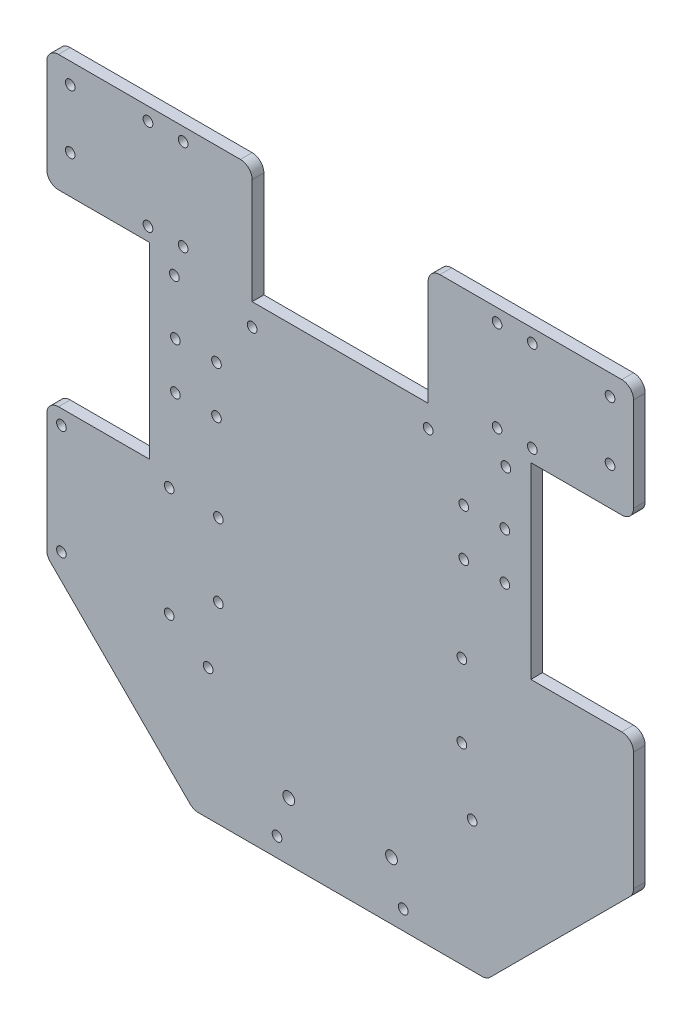
SolidWorks part; units mm, degrees
ref_plane "前视基准面" through (0, 0, 0) normal (0, 0, 1) x (1, 0, 0)
ref_plane "上视基准面" through (0, 0, 0) normal (0, 1, 0) x (1, 0, 0)
ref_plane "右视基准面" through (0, 0, 0) normal (1, 0, 0) x (0, 0, -1)
sketch "草图1" plane through (0, 0, 0) normal (0, 0, 1) x (1, 0, 0)
  line L0 (0, 0) -> (0, 207.9951) construction
  line L1 (-96, 200) -> (-30, 200)
  line L2 (-100, 196) -> (-100, 160)
  line L3 (-50, 0) -> (50, 0)
  line L4 (100, 196) -> (100, 160)
  line L5 (-100, 200) -> (74.6614, 24.6614) construction
  line L6 (-75.1068, 25.1068) -> (100, 200) construction
  line L7 (30, 200) -> (96, 200)
  line L8 (-30, 160) -> (30, 160)
  line L9 (-30, 160) -> (-30, 200)
  line L11 (30, 160) -> (30, 200)
  line L12 (-30, 160) -> (30, 200) construction
  line L13 (-30, 200) -> (30, 160) construction
  line L14 (100, 96) -> (65, 96)
  line L15 (-100, 160) -> (-65, 160)
  line L17 (-100, 96) -> (-65, 96)
  line L18 (-65, 160) -> (-65, 96)
  line L19 (65, 160) -> (65, 96)
  line L20 (100, 160) -> (65, 160)
  line L22 (-100, 96) -> (-100, 50)
  line L23 (100, 96) -> (100, 50)
  line L24 (-100, 50) -> (-50, 0)
  line L25 (100, 50) -> (50, 0)
  arc A0 (96, 200) -> (100, 196) centre (96, 196) cw
  arc A1 (-96, 200) -> (-100, 196) centre (-96, 196) ccw
  point P0 (-0.2545, 99.8678)
  point P7 (0, 180)
  dimension "D9" = 4
  dimension "D1" = 46
  dimension "D2" = 200
  dimension "D3" = 60
  dimension "D4" = 40
  dimension "D5" = 64
  dimension "D6" = 35
  dimension "D7" = 200
  dimension "D8" = 135
extrude "凸台-拉伸1" add sketch "草图1" along normal blind 4
sketch "草图4" plane through (0, 0, 0) normal (0, 0, -1) x (-1, 0, 0)
  line L1 (65, 160) -> (-65, 160) construction
  line L2 (65, 160) -> (65, 39) construction
  line L3 (65, 39) -> (-65, 39) construction
  line L4 (-65, 160) -> (-65, 39) construction
  line L5 (56.5, 154.5) -> (-56.5, 154.5) construction
  line L6 (56.5, 154.5) -> (56.5, 44.5) construction
  line L7 (56.5, 44.5) -> (-56.5, 44.5) construction
  line L8 (-56.5, 154.5) -> (-56.5, 44.5) construction
  line L10 (-30, 160) -> (30, 160) construction
  line L12 (65, 160) -> (65, 96) construction
  line L13 (-65, 96) -> (-65, 160) construction
  line L14 (0, 0) -> (0, 62.8556) construction
  circle A0 centre (56.5, 154.5) radius 1.65
  circle A1 centre (-56.5, 154.5) radius 1.65
  circle A4 centre (45, 44.5) radius 1.65
  circle A5 centre (-45, 44.5) radius 1.65
  dimension "D6" = 3.3
  dimension "D7" = 3.3
  dimension "D1" = 110
  dimension "D2" = 5.5
  dimension "D3" = 8.5
  dimension "D4" = 8.5
  dimension "D5" = 5.5
  dimension "D8" = 90
extrude "切除-拉伸5" cut sketch "草图4" against normal blind 10
sketch "草图5" plane through (0, 0, 0) normal (0, 0, -1) x (-1, 0, 0)
  line L0 (0, 0) -> (0, 78) construction
  line L1 (41.5, 90.5) -> (-41.5, 90.5) construction
  line L2 (41.5, 90.5) -> (41.5, 65.5) construction
  line L3 (41.5, 65.5) -> (-41.5, 65.5) construction
  line L4 (-41.5, 90.5) -> (-41.5, 65.5) construction
  line L5 (41.5, 90.5) -> (-41.5, 65.5) construction
  line L6 (41.5, 65.5) -> (-41.5, 90.5) construction
  line L7 (50, 0) -> (-50, 0) construction
  circle A0 centre (41.5, 90.5) radius 1.65
  circle A1 centre (-41.5, 90.5) radius 1.65
  circle A2 centre (41.5, 65.5) radius 1.65
  circle A3 centre (-41.5, 65.5) radius 1.65
  point P0 (0, 78)
  dimension "D4" = 3.3
  dimension "D1" = 65.5
  dimension "D2" = 83
  dimension "D3" = 25
extrude "切除-拉伸6" cut sketch "草图5" against normal blind 10
sketch "草图6" plane through (0, 0, 0) normal (0, 0, -1) x (-1, 0, 0)
  line L1 (58.26, 91) -> (95, 91) construction
  line L2 (58.26, 91) -> (58.26, 53.62) construction
  line L3 (58.26, 53.62) -> (95, 53.62) construction
  line L4 (95, 91) -> (95, 53.62) construction
  line L5 (65, 96) -> (100, 96) construction
  line L6 (100, 96) -> (100, 50) construction
  circle A1 centre (58.26, 91) radius 1.65
  circle A2 centre (95, 91) radius 1.65
  circle A3 centre (58.26, 53.62) radius 1.65
  circle A4 centre (95, 53.62) radius 1.65
  dimension "D3" = 5
  dimension "D5" = 3.3
  dimension "D1" = 37.38
  dimension "D2" = 36.74
  dimension "D4" = 5
extrude "切除-拉伸7" cut sketch "草图6" against normal blind 10
sketch "草图7" plane through (0, 0, 0) normal (0, 0, -1) x (-1, 0, 0)
  line L0 (0, 0) -> (0, 6.5) construction
  line L1 (50, 0) -> (-50, 0) construction
  line L2 (-21.5, 6.5) -> (21.5, 6.5) construction
  circle A0 centre (-21.5, 6.5) radius 1.65
  circle A1 centre (21.5, 6.5) radius 1.65
  dimension "D3" = 3.3
  dimension "D1" = 6.5
  dimension "D2" = 43
extrude "切除-拉伸8" cut sketch "草图7" against normal blind 10
sketch "草图8" plane through (0, 0, 0) normal (0, 0, -1) x (-1, 0, 0)
  line L0 (0, 0) -> (0, 19.75) construction
  line L1 (-17.5, 19.75) -> (17.5, 19.75) construction
  circle A0 centre (-17.5, 19.75) radius 2
  circle A1 centre (17.5, 19.75) radius 2
  dimension "D3" = 4
  dimension "D1" = 19.75
  dimension "D2" = 35
extrude "切除-拉伸9" cut sketch "草图8" against normal blind 10
sketch "草图9" plane through (0, 0, 0) normal (0, 0, -1) x (-1, 0, 0)
  line L0 (0, 160) -> (0, 152.5) construction
  line L1 (-30, 160) -> (30, 160) construction
  line L2 (-30, 152.5) -> (30, 152.5) construction
  circle A0 centre (-30, 152.5) radius 1.65
  circle A1 centre (30, 152.5) radius 1.65
  dimension "D2" = 3.3
  dimension "D1" = 60
  dimension "D3" = 7.5
extrude "切除-拉伸10" cut sketch "草图9" against normal blind 10
sketch "草图10" plane through (0, 0, 4) normal (0, 0, 1) x (1, 0, 0)
  line L1 (-100, 196) -> (-100, 160) construction
  line L2 (-100, 193) -> (-92, 193) construction
  line L3 (-92, 193) -> (-92, 173) construction
  line L4 (0, 160) -> (0, 0) construction
  line L5 (30, 160) -> (-30, 160) construction
  line L6 (-30, 200) -> (-96, 200) construction
  circle A0 centre (-92, 193) radius 1.65
  circle A1 centre (-92, 173) radius 1.65
  circle A2 centre (92, 173) radius 1.65
  circle A3 centre (92, 193) radius 1.65
  dimension "D3" = 3.3
  dimension "D5" = 3.3
  dimension "D2" = 8
  dimension "D4" = 20
  dimension "D6" = 7
extrude "切除-拉伸11" cut sketch "草图10" against normal blind 10
sketch "草图11" plane through (0, 0, 4) normal (0, 0, 1) x (1, 0, 0)
  line L0 (96, 200) -> (30, 200) construction
  line L1 (65.5, 164.5) -> (53.5, 164.5) construction
  line L2 (65.5, 164.5) -> (65.5, 195.5) construction
  line L3 (65.5, 195.5) -> (53.5, 195.5) construction
  line L4 (53.5, 164.5) -> (53.5, 195.5) construction
  line L5 (65.5, 164.5) -> (53.5, 195.5) construction
  line L6 (65.5, 195.5) -> (53.5, 164.5) construction
  line L7 (30, 200) -> (30, 160) construction
  line L8 (0, 0) -> (0, 212.3238) construction
  line L9 (-50, 0) -> (50, 0) construction
  line L10 (-65.5, 195.5) -> (-53.5, 164.5) construction
  line L11 (-65.5, 164.5) -> (-53.5, 195.5) construction
  line L12 (-53.5, 164.5) -> (-53.5, 195.5) construction
  line L13 (-65.5, 195.5) -> (-53.5, 195.5) construction
  line L15 (-65.5, 164.5) -> (-65.5, 195.5) construction
  line L16 (-65.5, 164.5) -> (-53.5, 164.5) construction
  circle A0 centre (65.5, 164.5) radius 1.65
  circle A1 centre (53.5, 164.5) radius 1.65
  circle A2 centre (53.5, 195.5) radius 1.65
  circle A3 centre (65.5, 195.5) radius 1.65
  circle A8 centre (-65.5, 195.5) radius 1.65
  circle A9 centre (-53.5, 195.5) radius 1.65
  circle A10 centre (-53.5, 164.5) radius 1.65
  circle A11 centre (-65.5, 164.5) radius 1.65
  dimension "D1" = 3.3
  dimension "D2" = 4.5
  dimension "D3" = 31
  dimension "D4" = 12
  dimension "D5" = 23.5
extrude "切除-拉伸12" cut sketch "草图11" against normal blind 10
sketch "草图12" plane through (0, 0, 4) normal (0, 0, 1) x (1, 0, 0)
  line L0 (100, 96) -> (65, 96) construction
  line L1 (56.15, 136) -> (42.15, 136) construction
  line L2 (56.15, 136) -> (56.15, 120) construction
  line L3 (56.15, 120) -> (42.15, 120) construction
  line L4 (42.15, 136) -> (42.15, 120) construction
  line L5 (56.15, 136) -> (42.15, 120) construction
  line L6 (56.15, 120) -> (42.15, 136) construction
  line L8 (100, 160) -> (100, 196) construction
  line L9 (0, 0) -> (0, 113.8804) construction
  line L10 (-50, 0) -> (50, 0) construction
  line L11 (-56.15, 120) -> (-42.15, 136) construction
  line L12 (-56.15, 136) -> (-42.15, 120) construction
  line L13 (-42.15, 136) -> (-42.15, 120) construction
  line L14 (-56.15, 120) -> (-42.15, 120) construction
  line L15 (-56.15, 136) -> (-56.15, 120) construction
  line L16 (-56.15, 136) -> (-42.15, 136) construction
  circle A0 centre (56.15, 120) radius 1.65
  circle A1 centre (42.15, 120) radius 1.65
  circle A2 centre (42.15, 136) radius 1.65
  circle A3 centre (56.15, 136) radius 1.65
  circle A4 centre (-56.15, 136) radius 1.65
  circle A5 centre (-42.15, 136) radius 1.65
  circle A6 centre (-42.15, 120) radius 1.65
  circle A7 centre (-56.15, 120) radius 1.65
  point P0 (49.15, 128)
  point P25 (-49.15, 128)
  dimension "D3" = 3.3
  dimension "D1" = 14
  dimension "D2" = 16
  dimension "D4" = 32
  dimension "D5" = 43.85
extrude "切除-拉伸13" cut sketch "草图12" against normal blind 10
fillet "圆角1" radius 4 8 edges at (100, 96, 2) (100, 160, 2) (100, 50, 2) (50, 0, 2) (-50, 0, 2) (-100, 50, 2) (-100, 96, 2) (-100, 160, 2)
fillet "圆角2" radius 4 2 edges at (30, 200, 2) (-30, 200, 2)
